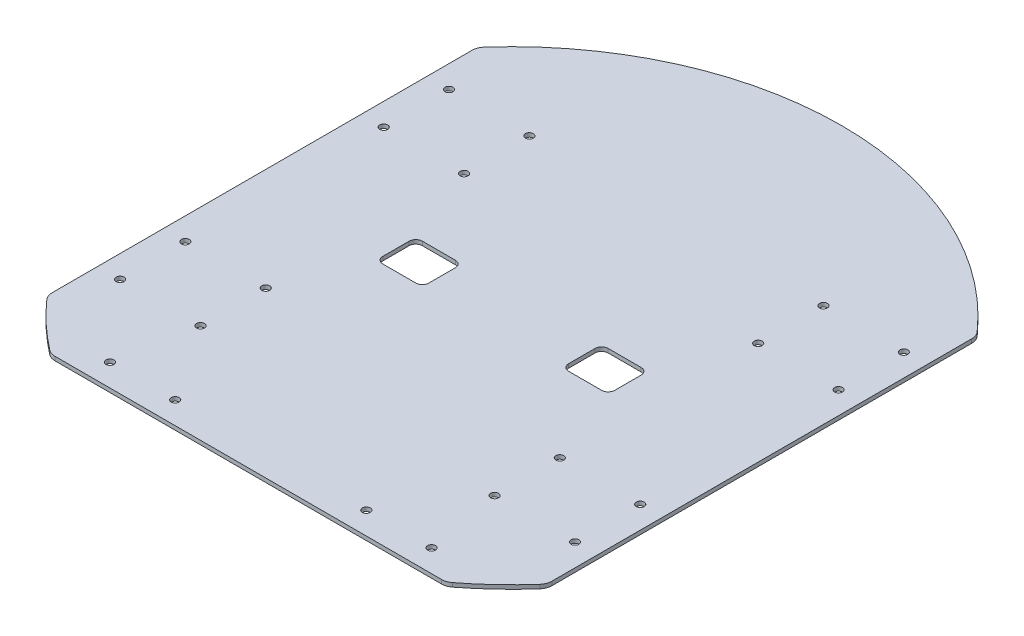
SolidWorks part; units mm, degrees
material "Acrylic (Medium-high impact)"
ref_plane "Front Plane" through (0, 0, 0) normal (0, 0, 1) x (1, 0, 0)
ref_plane "Top Plane" through (0, 0, 0) normal (0, 1, 0) x (1, 0, 0)
ref_plane "Right Plane" through (0, 0, 0) normal (1, 0, 0) x (0, 0, -1)
sketch "Sketch1" plane through (0, 0, 0) normal (0, 1, 0) x (1, 0, 0)
  line L4 (250, 0) -> (-250, 0) construction
  line L5 (0, 250) -> (0, -250) construction
  line L6 (-88, -10) -> (-88, 10)
  line L19 (53, 10) -> (53, -10)
  line L20 (58, -15) -> (83, -15)
  line L21 (88, -10) -> (88, 10)
  line L22 (83, 15) -> (58, 15)
  line L27 (-58, -15) -> (-83, -15)
  line L28 (-53, 10) -> (-53, -10)
  line L29 (-83, 15) -> (-58, 15)
  line L32 (-249.5496, 15) -> (-189.5496, 15)
  line L33 (-249.5496, 15) -> (-249.5496, 163.006)
  line L34 (-249.5496, 163.006) -> (-189.5496, 163.006)
  line L35 (-189.5496, 15) -> (-189.5496, 163.006)
  line L38 (-249.5496, -163.006) -> (-189.5496, -163.006)
  line L39 (-189.5496, -15) -> (-189.5496, -163.006)
  line L40 (-249.5496, -15) -> (-189.5496, -15)
  line L41 (-249.5496, -15) -> (-249.5496, -163.006)
  line L42 (249.5496, 163.006) -> (189.5496, 163.006)
  line L43 (189.5496, 15) -> (189.5496, 163.006)
  line L44 (249.5496, 15) -> (189.5496, 15)
  line L45 (249.5496, 15) -> (249.5496, 163.006)
  line L46 (249.5496, -15) -> (249.5496, -163.006)
  line L47 (249.5496, -15) -> (189.5496, -15)
  line L48 (189.5496, -15) -> (189.5496, -163.006)
  line L49 (249.5496, -163.006) -> (189.5496, -163.006)
  line L50 (-150, -200) -> (150, -200)
  line L51 (189.5496, 15) -> (189.5496, -15)
  line L52 (-189.5496, 15) -> (-189.5496, -15)
  line L53 (-273.3512, 89.003) -> (-105.748, 89.003) construction
  arc A0 (249.5496, -15) -> (249.5496, 15) centre (0, 0) ccw
  arc A9 (53, -10) -> (58, -15) centre (58, -10) ccw
  arc A10 (83, -15) -> (88, -10) centre (83, -10) ccw
  arc A11 (88, 10) -> (83, 15) centre (83, 10) ccw
  arc A12 (53, 10) -> (58, 15) centre (58, 10) cw
  arc A17 (-83, -15) -> (-88, -10) centre (-83, -10) cw
  arc A18 (-53, -10) -> (-58, -15) centre (-58, -10) cw
  arc A19 (-88, 10) -> (-83, 15) centre (-83, 10) cw
  arc A20 (-53, 10) -> (-58, 15) centre (-58, 10) ccw
  arc A29 (-189.5496, -163.006) -> (189.5496, -163.006) centre (0, 0) ccw
  arc A30 (189.5496, 163.006) -> (-189.5496, 163.006) centre (0, 0) ccw
  arc A31 (-249.5496, -15) -> (-249.5496, 15) centre (0, 0) cw
  point P20 (-194.5622, -69.4579)
  point P21 (-219.5496, 83.6935)
  point P52 (70.5, -15)
  point P53 (53, 0)
  point P68 (-189.5496, 89.003)
  point P87 (0, 0)
  dimension "D1" = 500
  dimension "D2" = 53
  dimension "D7" = 5
  dimension "D12" = 50
  dimension "D4" = 60
  dimension "D5" = 15
  dimension "D8" = 30
  dimension "D9" = 35
extrude "Boss-Extrude1" add sketch "Sketch1" along normal blind 3 contours L32 A0 L35 A20 L28 A18 L27 A17 L6 A19 L29 L19 A12 L22 A11 L21 A10 L20 A9
fillet "Fillet1" radius 10 6 edges at (-189.5496, 1.5, -163.006) (150, 1.5, 200) (-150, 1.5, 200) (-189.5496, 1.5, 163.006) (189.5496, 1.5, 163.006) (189.5496, 1.5, -163.006)
sketch "Sketch2" plane through (0, 0, 0) normal (0, -1, 0) x (1, 0, 0)
  line L0 (-252.4877, -100) -> (-92.6115, -100) construction
  line L2 (-172.5496, -124.75) -> (-172.5496, -75.25) construction
  line L3 (-189.5496, 159.2543) -> (-189.5496, -159.2543) construction
  line L4 (-111.5496, -124.75) -> (-111.5496, -75.25) construction
  line L5 (0, -285.8013) -> (0, 685.8013) construction
  line L6 (248.8499, 0) -> (-252.4877, 0) construction
  line L7 (140, 200) -> (-140, 200) construction
  line L8 (-146.6288, 200) -> (146.6288, 200) construction
  line L9 (-83, -15) -> (-58, -15) construction
  circle A0 centre (-172.5496, -124.75) radius 3
  circle A1 centre (-172.5496, -75.25) radius 3
  circle A2 centre (-111.5496, -124.75) radius 3
  circle A3 centre (-111.5496, -75.25) radius 3
  circle A4 centre (111.5496, -75.25) radius 3
  circle A5 centre (172.5496, -75.25) radius 3
  circle A6 centre (172.5496, -124.75) radius 3
  circle A7 centre (111.5496, -124.75) radius 3
  circle A8 centre (172.5496, 75.25) radius 3
  circle A9 centre (172.5496, 124.75) radius 3
  circle A10 centre (111.5496, 124.75) radius 3
  circle A11 centre (111.5496, 75.25) radius 3
  circle A12 centre (-172.5496, 75.25) radius 3
  circle A13 centre (-111.5496, 75.25) radius 3
  circle A14 centre (-111.5496, 124.75) radius 3
  circle A15 centre (-172.5496, 124.75) radius 3
  circle A16 centre (-122, 183) radius 3
  circle A17 centre (-72.5, 183) radius 3
  circle A18 centre (72.5, 183) radius 3
  circle A19 centre (122, 183) radius 3
  point P7 (-172.5496, -100)
  point P28 (0, 200)
  dimension "D4" = 6
  dimension "D5" = 85
  dimension "D13" = 6
  dimension "D14" = 49.5
  dimension "D2" = 49.5
  dimension "D3" = 17
  dimension "D6" = 61
  dimension "D9" = 280
  dimension "D10" = 0
  dimension "D11" = 17
  dimension "D12" = 18
extrude "Cut-Extrude1" cut sketch "Sketch2" against normal through all both and the other way through all
